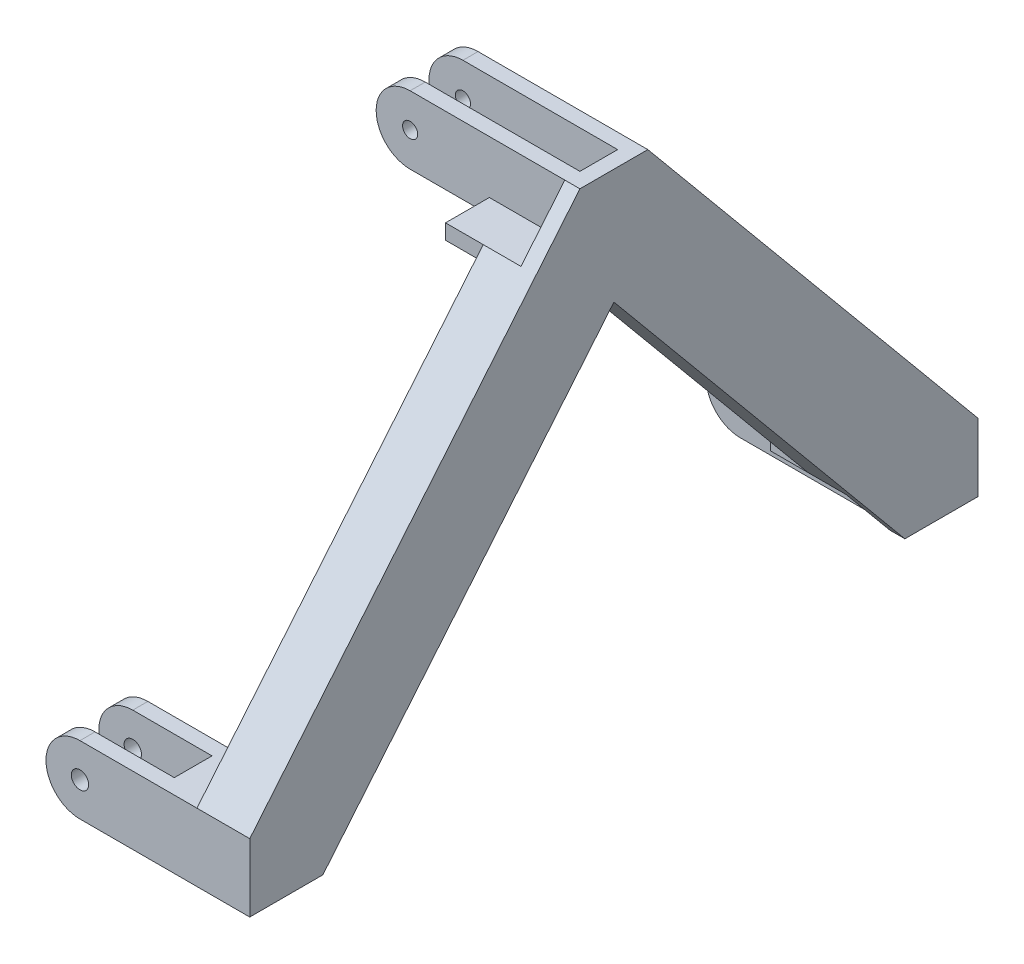
SolidWorks part; units mm, degrees
other "Markup1"
sketch "Sketch7" plane through (-150, 547, -482.5) normal (-0.7837, 0.5348, -0.3159) x (-0.4255, -0.0917, 0.9003)
material "AISI 4340 Steel, normalized"
ref_plane "Front Plane" through (0, 0, 0) normal (0, 0, 1) x (1, 0, 0)
ref_plane "Top Plane" through (0, 0, 0) normal (0, 1, 0) x (1, 0, 0)
ref_plane "Right Plane" through (0, 0, 0) normal (1, 0, 0) x (0, 0, -1)
sketch "Sketch1" plane through (0, 0, 0) normal (1, 0, 0) x (0, 0, -1)
  line L0 (-462.5, 0) -> (-412.5, 0)
  line L1 (0, -179.0012) -> (0, 585.1654) construction
  line L2 (-327.5, 0) -> (-327.5, 20)
  line L3 (-327.5, 20) -> (-482.5, 20)
  line L4 (-482.5, 20) -> (-482.5, -70)
  line L6 (-482.5, -70) -> (-462.5, -70)
  line L7 (-462.5, -70) -> (-462.5, 0)
  line L8 (-412.5, 0) -> (-412.5, -70)
  line L9 (-412.5, -70) -> (-392.5, -70)
  line L10 (-392.5, -70) -> (-392.5, 0)
  line L11 (-392.5, 0) -> (-327.5, 0)
  line L12 (25, 477) -> (-25, 477)
  line L13 (-103.112, 477) -> (-103.112, 457)
  line L14 (-103.112, 457) -> (103.112, 457)
  line L15 (-45, 477) -> (-45, 547)
  line L16 (-45, 547) -> (-25, 547)
  line L17 (-25, 547) -> (-25, 477)
  line L18 (-45, 477) -> (-103.112, 477)
  line L19 (45, 477) -> (103.112, 477)
  line L20 (25, 547) -> (25, 477)
  line L21 (45, 547) -> (25, 547)
  line L22 (45, 477) -> (45, 547)
  line L23 (103.112, 477) -> (103.112, 457)
  line L24 (392.5, 0) -> (327.5, 0)
  line L25 (392.5, -70) -> (392.5, 0)
  line L26 (412.5, -70) -> (392.5, -70)
  line L27 (412.5, 0) -> (412.5, -70)
  line L28 (462.5, -70) -> (462.5, 0)
  line L29 (482.5, -70) -> (462.5, -70)
  line L30 (482.5, 20) -> (482.5, -70)
  line L31 (327.5, 20) -> (482.5, 20)
  line L32 (327.5, 0) -> (327.5, 20)
  line L33 (462.5, 0) -> (412.5, 0)
  line L34 (-482.5, 20) -> (-45, 547) construction
  point P16 (0, 477)
  point P27 (0, 457)
  point P37 (-103.8427, 476.1197)
  dimension "D1" = 655
  dimension "D2" = 20
  dimension "D3" = 825
  dimension "D4" = 50
  dimension "D5" = 437
  dimension "D6" = 20
  dimension "D7" = 90
  dimension "D8" = 90
  dimension "D9" = 50
extrude "Boss-Extrude1" add sketch "Sketch1" along normal blind 100
sketch "Sketch2" plane through (0, 0, 0) normal (-1, 0, 0) x (0, 0, 1)
  line L0 (-482.5, -70) -> (-482.5, 20)
  line L1 (-482.5, 20) -> (-462.5, 20)
  line L2 (-482.5, 20) -> (-327.5, 20) construction
  line L3 (-462.5, 20) -> (-462.5, -70)
  line L4 (-462.5, -70) -> (-482.5, -70)
  line L5 (-462.5, 0) -> (-462.5, -70) construction
  line L6 (-412.5, -70) -> (-392.5, -70)
  line L7 (-392.5, -70) -> (-392.5, 20)
  line L8 (-392.5, 20) -> (-412.5, 20)
  line L9 (-412.5, 20) -> (-412.5, -70)
  line L10 (0, 0) -> (0, 241.8238) construction
  line L11 (-45, 547) -> (-25, 547)
  line L12 (-25, 547) -> (-25, 457)
  line L13 (103.112, 457) -> (-103.112, 457) construction
  line L14 (-25, 457) -> (-45, 457)
  line L15 (-45, 457) -> (-45, 547)
  line L16 (45, 457) -> (45, 547)
  line L17 (25, 457) -> (45, 457)
  line L18 (25, 547) -> (25, 457)
  line L19 (45, 547) -> (25, 547)
  line L20 (412.5, 20) -> (412.5, -70)
  line L21 (392.5, 20) -> (412.5, 20)
  line L22 (392.5, -70) -> (392.5, 20)
  line L23 (412.5, -70) -> (392.5, -70)
  line L24 (462.5, -70) -> (482.5, -70)
  line L25 (462.5, 20) -> (462.5, -70)
  line L26 (482.5, 20) -> (462.5, 20)
  line L27 (482.5, -70) -> (482.5, 20)
extrude "Boss-Extrude2" add sketch "Sketch2" along normal blind 150
sketch "Sketch3" plane through (100, 0, 0) normal (1, 0, 0) x (0, 0, -1)
  line L0 (0, 0) -> (0, 159.5705) construction
  line L1 (-482.5, -70) -> (-482.5, 20)
  line L2 (-482.5, 20) -> (-482.5, -70) construction
  line L3 (-482.5, 20) -> (-45, 547)
  line L4 (-45, 547) -> (45, 547)
  line L5 (-327.5, 0) -> (0, 394.4971)
  line L8 (327.5, 0) -> (0, 394.4971)
  line L9 (482.5, 20) -> (45, 547)
  line L12 (-392.5, -70) -> (-482.5, -70)
  line L14 (482.5, -70) -> (482.5, 20)
  line L15 (392.5, -70) -> (482.5, -70)
  line L18 (-327.5, 0) -> (-385.612, -70)
  line L19 (-385.612, -70) -> (-392.5, -70)
  line L20 (385.612, -70) -> (392.5, -70)
  line L21 (327.5, 0) -> (385.612, -70)
  point P18 (0, 547)
extrude "Boss-Extrude3" add sketch "Sketch3" along normal blind 20
sketch "Sketch4" plane through (0, 0, 482.5) normal (0, 0, 1) x (1, 0, 0)
  line L0 (100, 20) -> (-150, 20) construction
  line L1 (-150, -70) -> (-150, 20) construction
  line L2 (120, -70) -> (-150, -70) construction
  line L3 (-105, 20) -> (-150, 20)
  line L4 (-150, 20) -> (-150, -70)
  line L5 (-150, -70) -> (-105, -70)
  line L6 (100, 547) -> (-150, 547) construction
  line L7 (-150, 457) -> (0, 457) construction
  line L8 (-150, 457) -> (-150, 547) construction
  line L9 (-105, 457) -> (-150, 457)
  line L10 (-150, 457) -> (-150, 547)
  line L11 (-150, 547) -> (-105, 547)
  arc A0 (-105, 20) -> (-105, -70) centre (-105, -25) ccw
  circle A1 centre (-105, -25) radius 11.5
  arc A2 (-105, 547) -> (-105, 457) centre (-105, 502) ccw
  circle A3 centre (-105, 502) radius 10
  line M3 (100, 20) -> (-150, 20)
  line M4 (-150, 20) -> (-150, -70)
  line M5 (-150, -70) -> (120, -70)
  dimension "D1" = 23
  dimension "D2" = 20
extrude "Cut-Extrude2" cut sketch "Sketch4" against normal through all and the other way through all contours A0 M3 M4 | A1 | A0 L4 M5 | A3 | A2 L11 L10 | A2 L10 L9
sketch "Sketch5" plane through (100, 0, 0) normal (-1, 0, 0) x (0, 0, 1)
  line L7 (-482.5, 20) -> (-103.112, 477)
  line L10 (0, 0) -> (0, 90.9908) construction
  line L11 (-327.5, 0) -> (0, 394.4971)
  line L16 (-469.5031, 20) -> (-103.112, 461.3444)
  line L17 (-482.5, 20) -> (-327.5, 20) construction
  line L18 (-103.112, 457) -> (-103.112, 477) construction
  line L19 (-327.5, 15.6556) -> (0, 410.1528)
  line L20 (-327.5, 20) -> (-327.5, 0) construction
  line L21 (-327.5, 0) -> (-327.5, 15.6556)
  line L22 (-482.5, 20) -> (-469.5031, 20)
  line L23 (-103.112, 461.3444) -> (-103.112, 477)
  line L25 (482.5, 20) -> (469.5031, 20)
  line L26 (103.112, 461.3444) -> (103.112, 477)
  line L27 (482.5, 20) -> (103.112, 477)
  line L28 (469.5031, 20) -> (103.112, 461.3444)
  line L29 (327.5, 15.6556) -> (0, 410.1528)
  line L30 (327.5, 0) -> (327.5, 15.6556)
  line L31 (327.5, 0) -> (0, 394.4971)
  dimension "D1" = 10
  dimension "D2" = 10
extrude "Boss-Extrude4" add sketch "Sketch5" along normal blind 50 contours L19 L29 L30 L31 L11 L21 | L25 L28 L26 L27 | L23 L7 L22 L16
sketch "Sketch8" plane through (50, 0, 0) normal (-1, 0, 0) x (0, 0, 1)
  line L0 (-482.5, 20) -> (-327.5, 20)
  line L1 (-327.5, 20) -> (-327.5, 0)
  line L2 (-327.5, 0) -> (0, 394.4971)
  line L3 (0, 394.4971) -> (327.5, 0)
  line L4 (327.5, 0) -> (327.5, 20)
  line L5 (327.5, 20) -> (482.5, 20)
  line L6 (482.5, 20) -> (103.112, 477)
  line L7 (103.112, 477) -> (-103.112, 477)
  line L8 (-103.112, 477) -> (-482.5, 20)
extrude "Boss-Extrude5" add sketch "Sketch8" against normal blind 10
